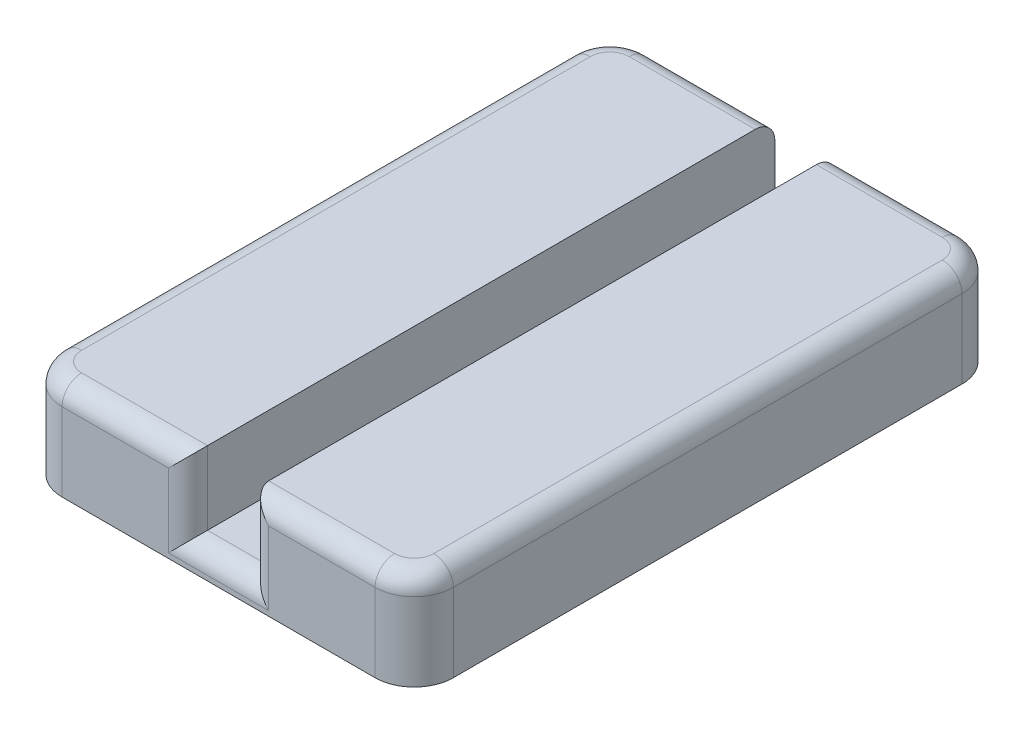
SolidWorks part; units mm, degrees
ref_plane "Front Plane" through (0, 0, 0) normal (0, 0, 1) x (1, 0, 0)
ref_plane "Top Plane" through (0, 0, 0) normal (0, 1, 0) x (1, 0, 0)
ref_plane "Right Plane" through (0, 0, 0) normal (1, 0, 0) x (0, 0, -1)
sketch "Sketch1" plane through (0, 0, 0) normal (0, 1, 0) x (1, 0, 0)
  line L0 (14.6844, 38.1) -> (22.86, 38.1)
  line L1 (2.54, 0) -> (22.86, 0)
  line L2 (0, 2.54) -> (0, 35.56)
  line L3 (2.54, 38.1) -> (10.7156, 38.1)
  line L4 (25.4, 2.54) -> (25.4, 35.56)
  line L6 (10.7156, 38.1) -> (10.7156, 31.75)
  line L7 (10.7156, 31.75) -> (14.6844, 31.75)
  line L8 (14.6844, 38.1) -> (14.6844, 31.75)
  arc A0 (22.86, 0) -> (25.4, 2.54) centre (22.86, 2.54) ccw
  arc A1 (2.54, 0) -> (0, 2.54) centre (2.54, 2.54) cw
  arc A2 (22.86, 38.1) -> (25.4, 35.56) centre (22.86, 35.56) cw
  arc A3 (0, 35.56) -> (2.54, 38.1) centre (2.54, 35.56) cw
  point P9 (0, 0)
  point P12 (25.4, 0)
  point P15 (0, 0)
  point P18 (25.4, 38.1)
  point P21 (0, 38.1)
  point P22 (0, 0)
  point P23 (0.0253, 35.9177)
  dimension "D7" = 2.54
  dimension "D1" = 3.9688
  dimension "D2" = 25.4
  dimension "D3" = 10.7156
  dimension "D5" = 6.35
  dimension "D6" = 38.1
extrude "Boss-Extrude1" add sketch "Sketch1" along normal blind 6.35 contours L2 A3 L3 L6 L7 L8 L0 A2 L4 A0 L1 A1
sketch "Sketch2" plane through (0, 6.35, 0) normal (0, 1, 0) x (1, 0, 0)
  line L0 (2.54, 0) -> (22.86, 0) construction
  line L1 (10.7156, 31.75) -> (14.6844, 31.75)
  line L2 (10.7156, 31.75) -> (10.7156, 0)
  line L3 (10.7156, 0) -> (14.6844, 0)
  line L4 (14.6844, 31.75) -> (14.6844, 0)
  line L5 (14.6844, 38.1) -> (14.6844, 31.75) construction
extrude "Cut-Extrude1" cut sketch "Sketch2" against normal blind 4.7625
fillet "Fillet1" radius 1.27 14 edges at (18.7722, 6.35, -38.1) (24.6561, 6.35, -37.3561) (25.4, 6.35, -19.05) (24.6561, 6.35, -0.7439) (6.6278, 6.35, -38.1) (0.7439, 6.35, -37.3561) (0, 6.35, -19.05) (0.7439, 6.35, -0.7439) (12.7, 1.5875, 0) (12.7, 1.5875, -31.75) (18.7722, 6.35, 0) (14.6844, 3.9688, 0) (10.7156, 3.9688, 0) (6.6278, 6.35, 0)
sketch "Sketch3" plane through (0, 0, 0) normal (0, -1, 0) x (1, 0, 0)
  line L0 (18.9237, -36.3631) -> (18.9237, -2.3212) construction
  text T0 "MIKO\r\nJIA\r\n5/32\r\n" font "Impact" height in points 16
  point P6 (0, 0)
  point P7 (1.5203, -2.4487)
  point P8 (0, 0)
  point P9 (0, 0)
  point P10 (1.906, -2.3212)
  point P11 (12.7401, -26.8007)
  point P12 (12.7401, -29.2869)
  point P13 (18.35, -36.3631)
extrude "Cut-Extrude2" cut sketch "Sketch3" against normal blind 0.7937
